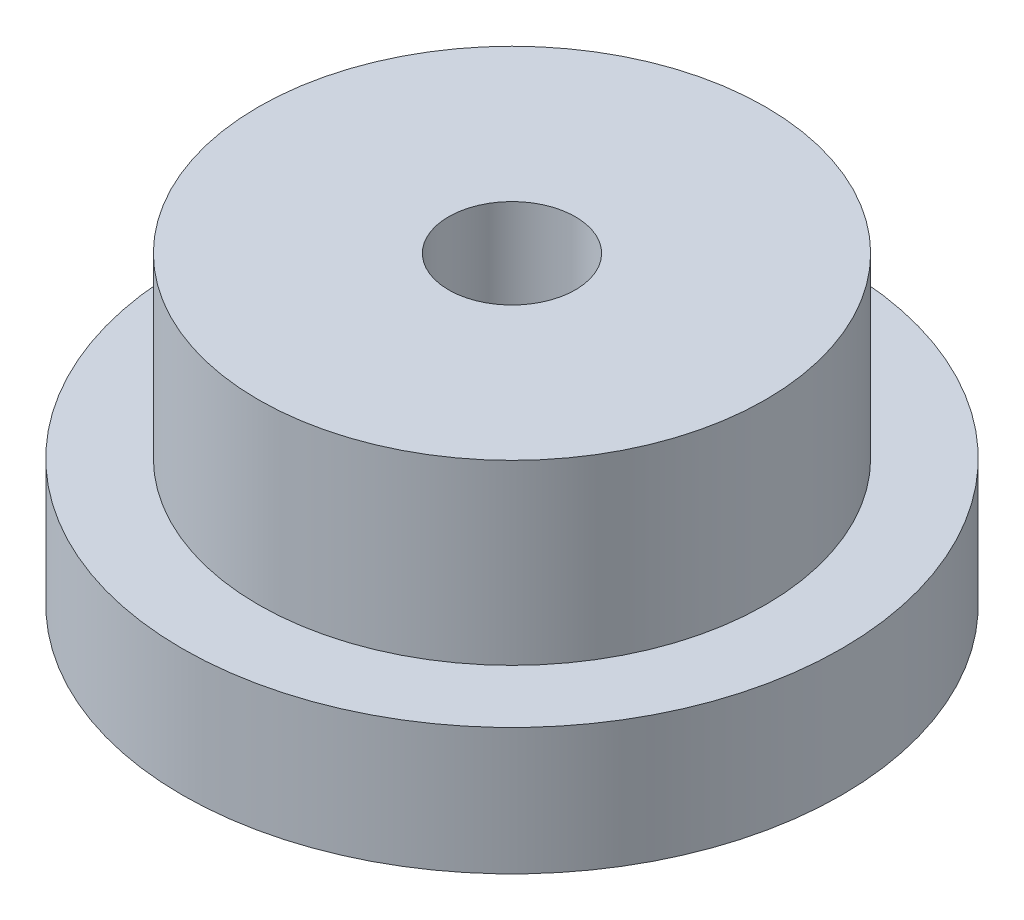
SolidWorks part; units mm, degrees
ref_plane "Front Plane" through (0, 0, 0) normal (0, 0, 1) x (1, 0, 0)
ref_plane "Top Plane" through (0, 0, 0) normal (0, 1, 0) x (1, 0, 0)
ref_plane "Right Plane" through (0, 0, 0) normal (1, 0, 0) x (0, 0, -1)
sketch "Sketch1" plane through (0, 0, 0) normal (0, 1, 0) x (1, 0, 0)
  circle A0 centre (0, 0) radius 13
  circle A1 centre (0, 0) radius 2.5
  dimension "D1" = 26
  dimension "D2" = 5
extrude "Boss-Extrude1" add sketch "Sketch1" along normal blind 5
sketch "Sketch2" plane through (0, 5, 0) normal (0, 1, 0) x (1, 0, 0)
  circle A0 centre (0, 0) radius 10
  circle A1 centre (0, 0) radius 2.5
  circle A2 centre (0, 0) radius 2.5 construction
  dimension "D1" = 20
extrude "Boss-Extrude2" add sketch "Sketch2" along normal blind 7
ref_plane "thread_mid" through (0, 2.5, 0) normal (0, 1, 0) x (1, 0, 0)
